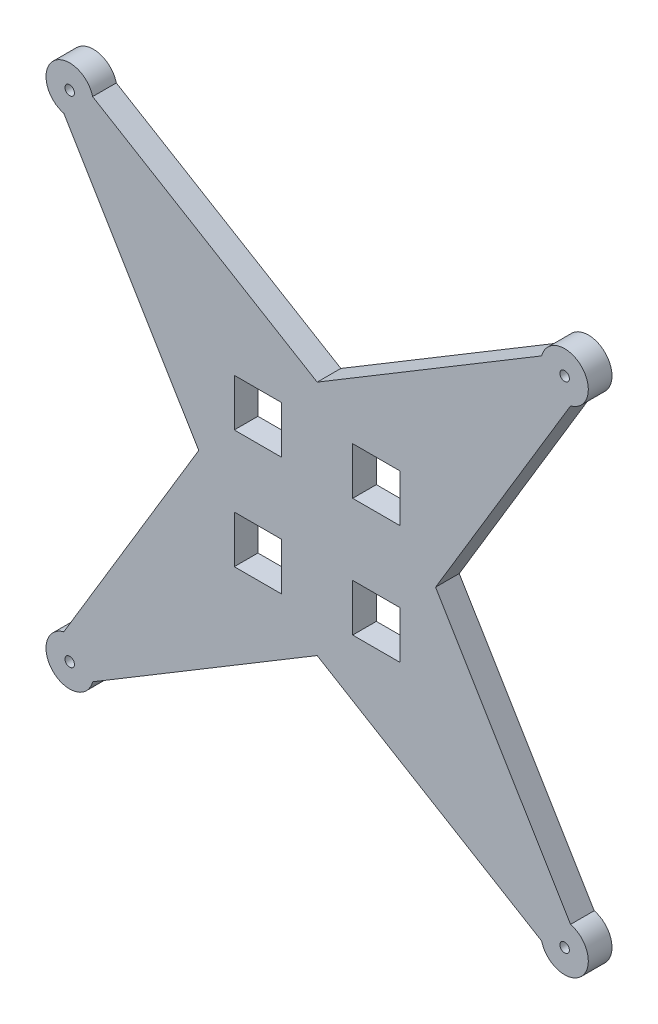
SolidWorks part; units mm, degrees
ref_plane "Front Plane" through (0, 0, 0) normal (0, 0, 1) x (1, 0, 0)
ref_plane "Top Plane" through (0, 0, 0) normal (0, 1, 0) x (1, 0, 0)
ref_plane "Right Plane" through (0, 0, 0) normal (1, 0, 0) x (0, 0, -1)
sketch "Esboço1" plane through (0, 0, 0) normal (0, 0, 1) x (1, 0, 0)
  line L0 (35, -15) -> (15, -15)
  line L4 (0, 50) -> (0, -50) construction
  line L5 (-50, 0) -> (50, 0) construction
  line L7 (50, 0) -> (-50, 0) construction
  line L13 (107, 94.8175) -> (50, 0)
  line L14 (50, 0) -> (107, -94.8175)
  line L16 (94.8175, -107) -> (0, -50)
  line L17 (0, -50) -> (-94.8175, -107)
  line L18 (-107, -94.8175) -> (-50, 0)
  line L19 (-50, 0) -> (-107, 94.8175)
  line L20 (-94.8175, 107) -> (0, 50)
  line L21 (0, 50) -> (94.8175, 107)
  line L22 (0, 50) -> (50, 0) construction
  line L23 (0, -50) -> (50, 0) construction
  line L24 (-50, 0) -> (0, -50) construction
  line L25 (0, 50) -> (-50, 0) construction
  line L26 (35, 25) -> (15, 25) construction
  line L27 (35, 35) -> (15, 35)
  line L28 (35, 35) -> (35, 15)
  line L29 (35, 15) -> (15, 15)
  line L30 (15, 35) -> (15, 15)
  line L31 (15, -35) -> (15, -15)
  line L32 (35, -35) -> (15, -35)
  line L33 (35, -35) -> (35, -15)
  line L34 (-35, 35) -> (-35, 15)
  line L35 (-15, 35) -> (-15, 15)
  line L36 (-15, -35) -> (-15, -15)
  line L37 (-35, -35) -> (-15, -35)
  line L38 (-35, -35) -> (-35, -15)
  line L39 (-35, -15) -> (-15, -15)
  line L40 (-35, 15) -> (-15, 15)
  line L41 (-35, 35) -> (-15, 35)
  arc A0 (-94.8175, 107) -> (-107, 94.8175) centre (-104.5, 104.5) ccw
  circle A1 centre (-104.5, 104.5) radius 2
  circle A2 centre (104.5, 104.5) radius 2
  arc A3 (94.8175, 107) -> (107, 94.8175) centre (104.5, 104.5) cw
  circle A4 centre (104.5, -104.5) radius 2
  arc A5 (94.8175, -107) -> (107, -94.8175) centre (104.5, -104.5) ccw
  circle A6 centre (-104.5, -104.5) radius 2
  arc A7 (-94.8175, -107) -> (-107, -94.8175) centre (-104.5, -104.5) cw
  point P18 (25, 25)
  point P21 (25, 25)
  dimension "D2" = 4
  dimension "D1" = 20
  dimension "D3" = 20
  dimension "D4" = 20
extrude "Ressalto-extrusão1" add sketch "Esboço1" along normal blind 10
sketch "Esboço3" plane through (0, 0, 0) normal (0, 0, -1) x (-1, 0, 0)
  line L0 (0, 50) -> (0, -50) construction
  line L1 (-50, 0) -> (50, 0) construction
  line L2 (50, 0) -> (107, -94.8175) construction
  circle A1 centre (-104.5, 104.5) radius 4.5
  circle A2 centre (-104.5, 104.5) radius 2 construction
  circle A3 centre (104.5, 104.5) radius 4.5
  circle A4 centre (104.5, -104.5) radius 4.5
  circle A5 centre (-104.5, -104.5) radius 4.5
  dimension "D1" = 9
extrude "Corte-extrusão1" cut sketch "Esboço3" against normal blind 4
